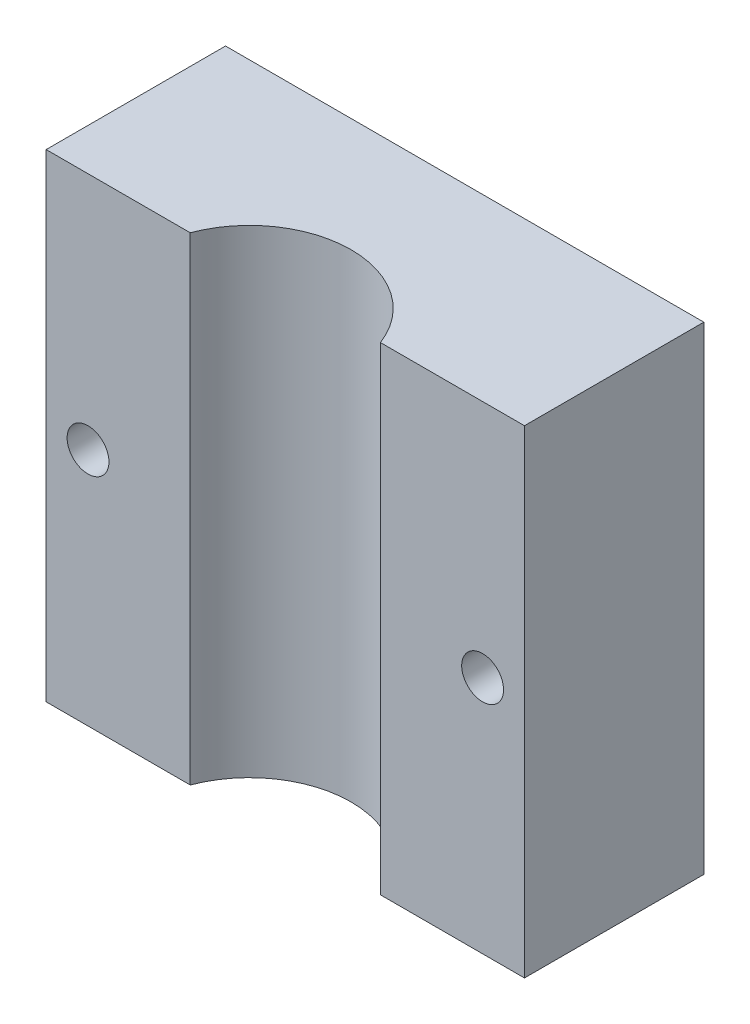
SolidWorks part; units mm, degrees
ref_plane "Front Plane" through (0, 0, 0) normal (0, 0, 1) x (1, 0, 0)
ref_plane "Top Plane" through (0, 0, 0) normal (0, 1, 0) x (1, 0, 0)
ref_plane "Right Plane" through (0, 0, 0) normal (1, 0, 0) x (0, 0, -1)
sketch "Sketch1" plane through (0, 0, 0) normal (0, 0, 1) x (1, 0, 0)
  line L1 (-20, 20) -> (20, 20)
  line L2 (-20, 20) -> (-20, -20)
  line L3 (-20, -20) -> (20, -20)
  line L4 (20, 20) -> (20, -20)
  line L5 (-20, 20) -> (20, -20) construction
  line L6 (-20, -20) -> (20, 20) construction
  point P0 (0, 0)
  dimension "D1" = 40
  dimension "D2" = 40
extrude "Boss-Extrude1" add sketch "Sketch1" along normal blind 15
sketch "Sketch2" plane through (0, 0, 15) normal (0, 0, 1) x (1, 0, 0)
  line L0 (20, 20) -> (-20, 20) construction
  line L1 (-20, 20) -> (-20, -20) construction
  line L2 (20, -20) -> (20, 20) construction
  circle A0 centre (-16.5, 0) radius 1.75
  circle A1 centre (16.5, 0) radius 1.75
  dimension "D3" = 3.5
  dimension "D4" = 3.5
  dimension "D1" = 20
  dimension "D2" = 20
  dimension "D5" = 3.5
  dimension "D6" = 3.5
extrude "Cut-Extrude1" cut sketch "Sketch2" against normal through all
sketch "Sketch3" plane through (0, 20, 0) normal (0, 1, 0) x (1, 0, 0)
  line L0 (20, -15) -> (-20, -15) construction
  line L2 (20, -15) -> (20, 0) construction
  circle A0 centre (0, -18) radius 8.5
  point P7 (20, -11.8628)
  dimension "D1" = 17
  dimension "D2" = 3
  dimension "D3" = 20
extrude "Cut-Extrude2" cut sketch "Sketch3" against normal through all
